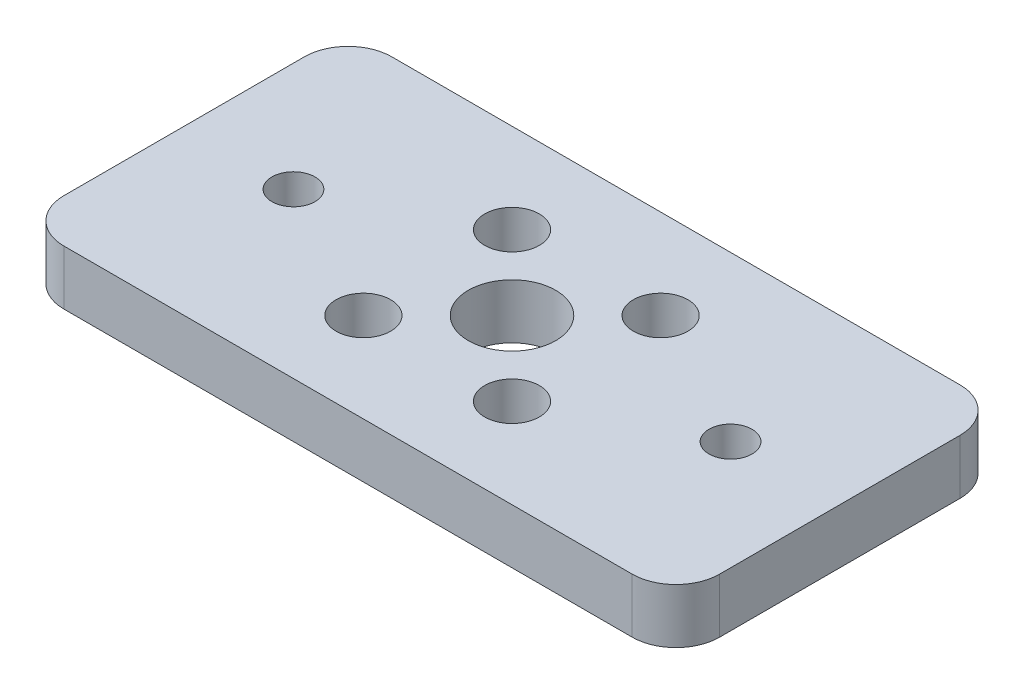
SolidWorks part; units mm, degrees
ref_plane "Front Plane" through (0, 0, 0) normal (0, 0, 1) x (1, 0, 0)
ref_plane "Top Plane" through (0, 0, 0) normal (0, 1, 0) x (1, 0, 0)
ref_plane "Right Plane" through (0, 0, 0) normal (1, 0, 0) x (0, 0, -1)
sketch "Sketch1" plane through (0, 0, 0) normal (0, 1, 0) x (1, 0, 0)
  line L1 (-19.05, -9.525) -> (19.05, -9.525)
  line L2 (-19.05, -9.525) -> (-19.05, 9.525)
  line L3 (-19.05, 9.525) -> (19.05, 9.525)
  line L4 (19.05, -9.525) -> (19.05, 9.525)
  line L5 (-19.05, -9.525) -> (19.05, 9.525) construction
  line L6 (-19.05, 9.525) -> (19.05, -9.525) construction
  circle A0 centre (0, 0) radius 2.54
  point P0 (0, 0)
  dimension "D3" = 5.08
  dimension "D1" = 19.05
  dimension "D2" = 38.1
extrude "Boss-Extrude1" add sketch "Sketch1" along normal blind 3.175
sketch "Sketch2" plane through (0, 3.175, 0) normal (0, 1, 0) x (1, 0, 0)
  line L1 (-4.318, -4.318) -> (4.318, -4.318) construction
  line L2 (-4.318, -4.318) -> (-4.318, 4.318) construction
  line L3 (-4.318, 4.318) -> (4.318, 4.318) construction
  line L4 (4.318, -4.318) -> (4.318, 4.318) construction
  line L5 (-4.318, -4.318) -> (4.318, 4.318) construction
  line L6 (-4.318, 4.318) -> (4.318, -4.318) construction
  circle A0 centre (-4.318, 4.318) radius 1.5875
  circle A1 centre (4.318, 4.318) radius 1.5875
  circle A2 centre (-4.318, -4.318) radius 1.5875
  circle A3 centre (4.318, -4.318) radius 1.5875
  point P0 (0, 0)
  dimension "D3" = 3.175
  dimension "D1" = 8.636
  dimension "D2" = 8.636
extrude "Cut-Extrude1" cut sketch "Sketch2" against normal through all
sketch "Sketch3" plane through (0, 3.175, 0) normal (0, 1, 0) x (1, 0, 0)
  line L0 (-12.7, 0) -> (12.7, 0) construction
  point P0 (-12.7, 0)
  point P1 (12.7, 0)
  point P2 (0, 0)
  point P8 (-12.7, 0)
  point P10 (12.7, 0)
  dimension "D1" = 25.4
hole_wizard "Ø2.5mm Dowel Hole1" positions "Sketch3" profile "Sketch4" hole size "Ø2.5" standard "ANSI Metric" end condition through all
sketch "Sketch4" plane through (12.7, 3.175, 0) normal (1, 0, 0) x (0, 0, 1)
  line L0 (0, 0) -> (0, 3.175)
  line L1 (0, 3.175) -> (1.25, 3.175)
  line L2 (1.25, 3.175) -> (1.25, 0)
  line L5 (1.25, 0) -> (0, 0)
  line L11 (0, -6.35) -> (0, 107.95) construction
  dimension "Thru Hole Dia." = 2.5
  dimension "Thru Hole Depth" = 3.175
fillet "Fillet1" radius 2.54 4 edges at (19.05, 1.5875, -9.525) (-19.05, 1.5875, -9.525) (-19.05, 1.5875, 9.525) (19.05, 1.5875, 9.525)
